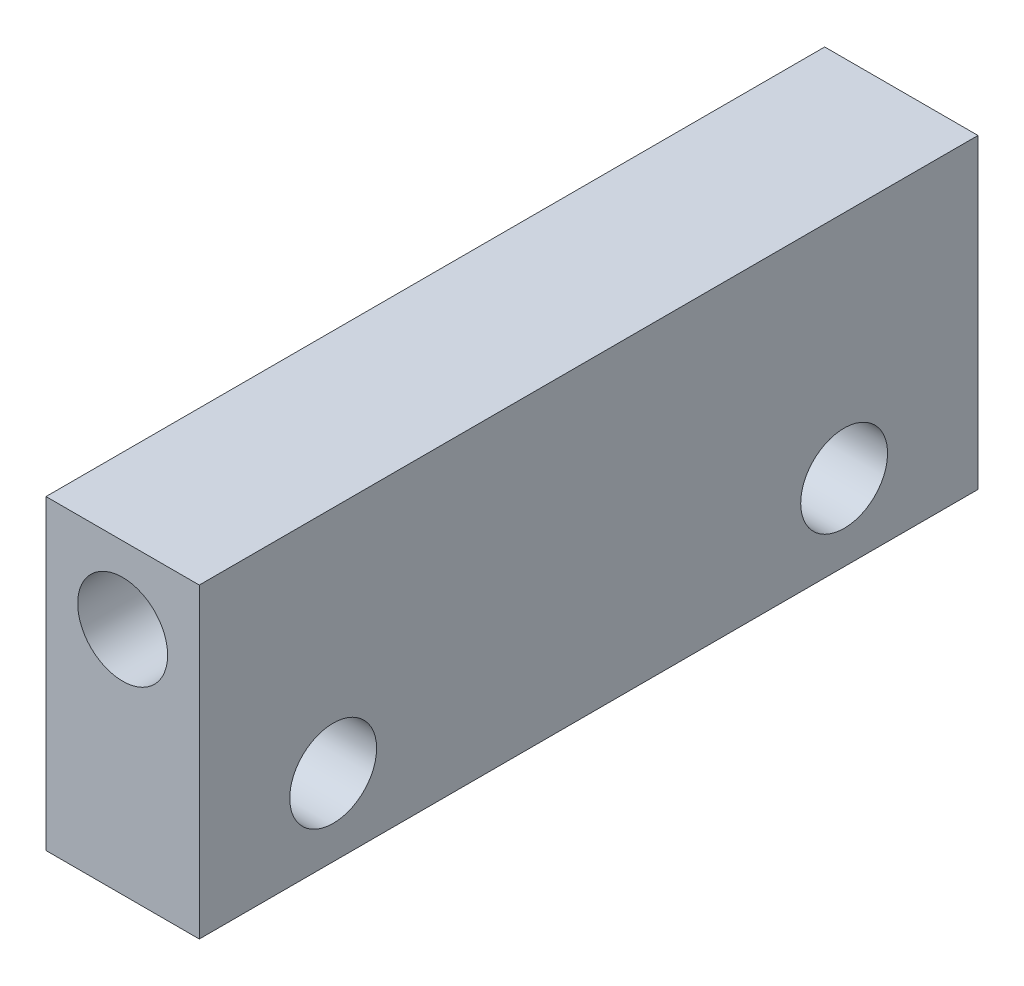
SolidWorks part; units mm, degrees
ref_plane "Front Plane" through (0, 0, 0) normal (0, 0, 1) x (1, 0, 0)
ref_plane "Top Plane" through (0, 0, 0) normal (0, 1, 0) x (1, 0, 0)
ref_plane "Right Plane" through (0, 0, 0) normal (1, 0, 0) x (0, 0, -1)
sketch "Sketch2" plane through (0, 0, 0) normal (0, 0, 1) x (1, 0, 0)
  line L0 (-10.954, 39.1928) -> (-10.954, 9.1928) construction
  line L1 (-18.454, 39.1928) -> (-3.454, 39.1928)
  line L2 (-18.454, 39.1928) -> (-18.454, 9.1928)
  line L3 (-18.454, 9.1928) -> (-3.454, 9.1928)
  line L4 (-3.454, 39.1928) -> (-3.454, 9.1928)
  line L5 (-10.954, 24.1928) -> (-3.454, 24.1928) construction
  circle A0 centre (-10.954, 31.6928) radius 4.4
  dimension "D3" = 8.8
  dimension "D4" = 7.5
  dimension "D1" = 15
  dimension "D2" = 30
extrude "Boss-Extrude1" add sketch "Sketch2" along normal blind 76.2
sketch "Sketch3" plane through (-3.454, 0, 0) normal (1, 0, 0) x (0, 0, -1)
  line L0 (-76.2, 24.1928) -> (0, 24.1928) construction
  line L1 (-76.2, 9.1928) -> (-76.2, 39.1928) construction
  line L2 (0, 9.1928) -> (0, 39.1928) construction
  line L3 (-38.1, 24.1928) -> (-38.1, 9.1928) construction
  line L4 (-76.2, 9.1928) -> (0, 9.1928) construction
  line L5 (-38.1, 16.6928) -> (-76.2, 16.6928) construction
  circle A0 centre (-63.1, 16.6928) radius 4.25
  circle A1 centre (-13.1, 16.6928) radius 4.25
  dimension "D1" = 8.5
  dimension "D2" = 50
  dimension "D3" = 76.2
extrude "Cut-Extrude2" cut sketch "Sketch3" against normal through all
